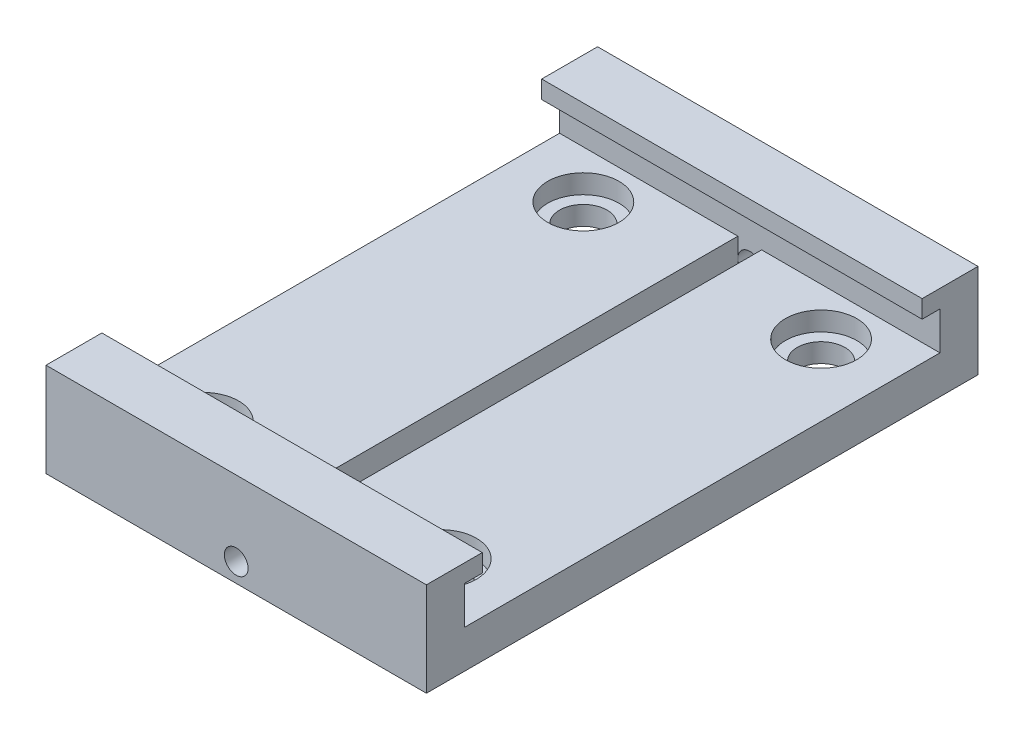
SolidWorks part; units mm, degrees
ref_plane "Front Plane" through (0, 0, 0) normal (0, 0, 1) x (1, 0, 0)
ref_plane "Top Plane" through (0, 0, 0) normal (0, 1, 0) x (1, 0, 0)
ref_plane "Right Plane" through (0, 0, 0) normal (1, 0, 0) x (0, 0, -1)
sketch "Sketch1" plane through (0, 0, 0) normal (0, 1, 0) x (1, 0, 0)
  line L1 (25.4, 36.83) -> (-25.4, 36.83)
  line L2 (25.4, 36.83) -> (25.4, -36.83)
  line L3 (25.4, -36.83) -> (-25.4, -36.83)
  line L4 (-25.4, 36.83) -> (-25.4, -36.83)
  line L5 (25.4, 36.83) -> (-25.4, -36.83) construction
  line L6 (25.4, -36.83) -> (-25.4, 36.83) construction
  point P0 (0, 0)
  dimension "D1" = 73.66
  dimension "D2" = 50.8
extrude "Boss-Extrude1" add sketch "Sketch1" along normal blind 25.4
sketch "Sketch4" plane through (25.4, 0, 0) normal (1, 0, 0) x (0, 0, -1)
  line L0 (-36.83, 0) -> (36.83, 0) construction
  line L1 (-31.75, 10.16) -> (31.75, 10.16)
  line L2 (-31.75, 10.16) -> (-31.75, 5.08)
  line L3 (-31.75, 5.08) -> (31.75, 5.08)
  line L4 (31.75, 10.16) -> (31.75, 5.08)
  line L5 (-31.75, 10.16) -> (31.75, 5.08) construction
  line L6 (-31.75, 5.08) -> (31.75, 10.16) construction
  line L9 (-29.3688, 10.16) -> (29.3688, 10.16)
  line L10 (-29.3688, 10.16) -> (-29.3688, 12.5412)
  line L11 (-29.3688, 12.5412) -> (29.3688, 12.5412)
  line L12 (29.3688, 10.16) -> (29.3688, 12.5412)
  point P0 (0, 7.62)
  point P5 (0, 12.5412)
  dimension "D1" = 5.08
  dimension "D2" = 63.5
  dimension "D3" = 2.3813
  dimension "D4" = 2.3813
  dimension "D5" = 5.08
extrude "Cut-Extrude3" cut sketch "Sketch4" against normal through all contours L4 L1 L2 L3 | L1 L12 L11 L10
sketch "Sketch5" plane through (25.4, 0, 0) normal (1, 0, 0) x (0, 0, -1)
  line L0 (36.83, 25.4) -> (36.83, 0) construction
  line L1 (-36.83, 25.4) -> (36.83, 25.4)
  line L2 (-36.83, 25.4) -> (-36.83, 12.5412)
  line L3 (-36.83, 12.5412) -> (36.83, 12.5412)
  line L4 (36.83, 25.4) -> (36.83, 12.5412)
  line L5 (-29.3688, 12.5412) -> (29.3688, 12.5412) construction
extrude "Cut-Extrude4" cut sketch "Sketch5" against normal through all
sketch "Sketch6" plane through (0, 5.08, 0) normal (0, 1, 0) x (1, 0, 0)
  line L0 (-25.4, 31.75) -> (25.4, 31.75) construction
  line L1 (-1.5875, 31.75) -> (1.5875, 31.75)
  line L2 (-1.5875, 31.75) -> (-1.5875, -31.75)
  line L3 (-1.5875, -31.75) -> (1.5875, -31.75)
  line L4 (1.5875, 31.75) -> (1.5875, -31.75)
  line L5 (-25.4, -31.75) -> (25.4, -31.75) construction
  point P8 (0, 31.75)
  dimension "D1" = 3.175
extrude "Cut-Extrude5" cut sketch "Sketch6" against normal through all
sketch "Sketch7" plane through (0, 5.08, 0) normal (0, 1, 0) x (1, 0, 0)
  line L0 (-15.875, 25.4) -> (15.875, 25.4) construction
  line L1 (-15.875, 25.4) -> (-15.875, -25.4) construction
  circle A0 centre (15.875, 25.4) radius 3.175
  circle A1 centre (-15.875, 25.4) radius 3.175
  circle A2 centre (-15.875, -25.4) radius 3.175
  circle A3 centre (15.875, -25.4) radius 3.175
  point P8 (0, 25.4)
  point P9 (-15.875, 0)
  dimension "D1" = 6.35
  dimension "D2" = 50.8
  dimension "D3" = 31.75
extrude "Cut-Extrude6" cut sketch "Sketch7" against normal through all
sketch "Sketch8" plane through (0, 5.08, 0) normal (0, 1, 0) x (1, 0, 0)
  circle A0 centre (-15.875, 25.4) radius 4.7625
  circle A1 centre (-15.875, -25.4) radius 4.7625
  circle A2 centre (15.875, -25.4) radius 4.7625
  circle A3 centre (15.875, 25.4) radius 4.7625
  dimension "D1" = 9.525
extrude "Cut-Extrude7" cut sketch "Sketch8" against normal blind 2.54
sketch "Sketch9" plane through (0, 0, 36.83) normal (0, 0, 1) x (1, 0, 0)
  line L0 (-25.4, 12.5412) -> (-25.4, 0) construction
  line L1 (-25.4, 5.08) -> (25.4, 5.08) construction
  line L2 (-25.4, 5.08) -> (-25.4, 0) construction
  line L3 (-25.4, 0) -> (25.4, 0) construction
  line L4 (25.4, 5.08) -> (25.4, 0) construction
  line L5 (7.3284, 5.08) -> (7.3284, 0) construction
  circle A0 centre (0, 2.54) radius 1.5875
  point P11 (0, 0)
  point P12 (7.3284, 2.54)
  point P13 (-0.1746, 2.54)
  point P15 (0, 0)
  dimension "D2" = 3.175
  dimension "D1" = 5.08
extrude "Cut-Extrude8" cut sketch "Sketch9" against normal up to surface (68.58 mm away)
mirror "Mirror1" about plane through (0, 0, 0) normal (0, 0, 1) of "Cut-Extrude8"
